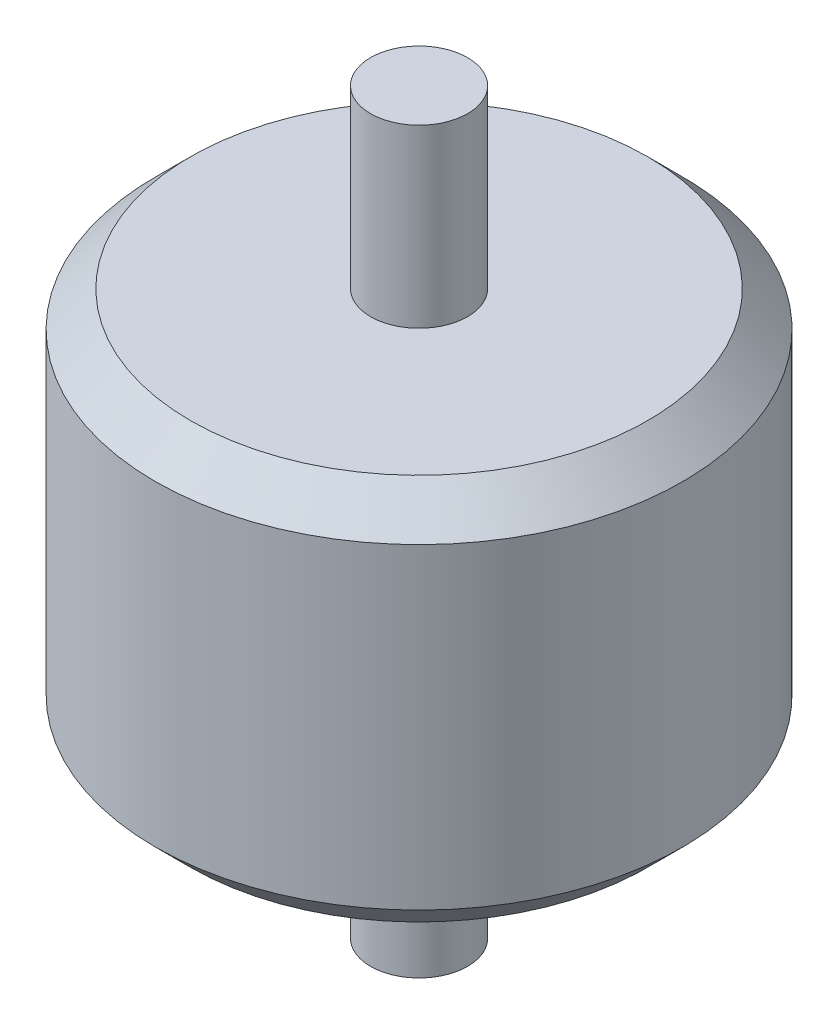
SolidWorks part; units mm, degrees
ref_plane "Front Plane" through (0, 0, 0) normal (0, 0, 1) x (1, 0, 0)
ref_plane "Top Plane" through (0, 0, 0) normal (0, 1, 0) x (1, 0, 0)
ref_plane "Right Plane" through (0, 0, 0) normal (1, 0, 0) x (0, 0, -1)
sketch "Sketch1" plane through (0, 0, 0) normal (1, 0, 0) x (0, 0, -1)
  line L0 (0, 0) -> (1.27, 1.27)
  line L1 (0, 0) -> (19.05, 0)
  line L2 (0, 0) -> (0, -11.43)
  line L3 (0, -11.43) -> (19.05, -11.43)
  line L4 (19.05, 0) -> (19.05, -11.43)
  line L5 (1.27, 1.27) -> (17.78, 1.27)
  line L6 (17.78, 1.27) -> (19.05, 0)
  line L7 (0, -11.43) -> (1.27, -12.7)
  line L8 (1.27, -12.7) -> (17.7837, -12.7)
  line L9 (17.7837, -12.7) -> (19.05, -11.43)
  line L10 (7.7724, -12.7) -> (7.7724, -19.05)
  line L11 (7.7724, 1.27) -> (11.2776, 1.27)
  line L12 (7.7724, 1.27) -> (7.7724, 7.62)
  line L13 (7.7724, 7.62) -> (11.2776, 7.62)
  line L14 (11.2776, 1.27) -> (11.2776, 7.62)
  line L15 (7.7724, -19.05) -> (11.2776, -19.05)
  line L16 (11.2776, -19.05) -> (11.2776, -12.7)
  line L17 (9.525, 7.62) -> (9.525, -24.2032)
  point P13 (9.525, 1.27)
  point P14 (9.525, 7.62)
  dimension "D1" = 19.05
  dimension "D2" = 11.43
  dimension "D3" = 1.27
  dimension "D4" = 45
  dimension "D5" = 45
  dimension "D6" = 1.27
  dimension "D7" = 45
  dimension "D8" = 45.084
  dimension "D9" = 3.5052
  dimension "D10" = 6.35
  dimension "D11" = 6.35
  dimension "D12" = 3.5052
revolve "Revolve1" add sketch "Sketch1" angle 360 about L17
